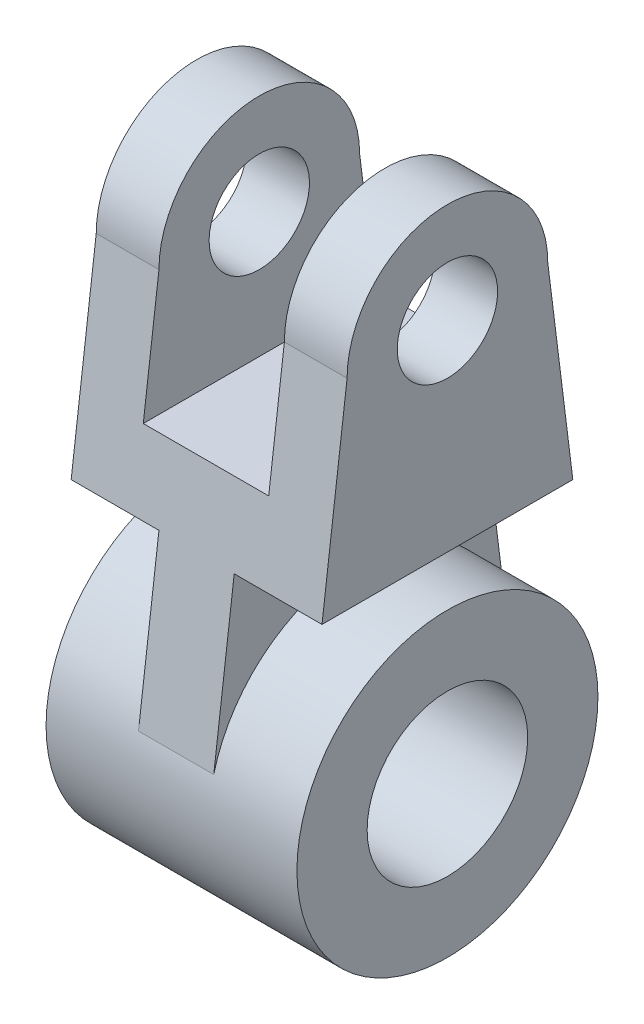
SolidWorks part; units mm, degrees
ref_plane "Front Plane" through (0, 0, 0) normal (0, 0, 1) x (1, 0, 0)
ref_plane "Top Plane" through (0, 0, 0) normal (0, 1, 0) x (1, 0, 0)
ref_plane "Right Plane" through (0, 0, 0) normal (1, 0, 0) x (0, 0, -1)
sketch "Sketch1" plane through (0, 0, 0) normal (1, 0, 0) x (0, 0, -1)
  circle A0 centre (0, 0) radius 30
  circle A1 centre (0, 0) radius 16
  dimension "D1" = 32
  dimension "D2" = 60
extrude "Boss-Extrude1" add sketch "Sketch1" along normal mid plane 50
sketch "Sketch2" plane through (0, 0, 0) normal (1, 0, 0) x (0, 0, -1)
  line L0 (0, 30) -> (0, 40)
  circle A0 centre (0, 0) radius 30 construction
  dimension "D1" = 10
ref_plane "Plane1" through (0, 40, 0) normal (0, 1, 0) x (1, 0, 0)
sketch "Sketch3" plane through (0, 40, 0) normal (0, 1, 0) x (1, 0, 0)
  line L1 (-25, 25) -> (25, 25)
  line L2 (-25, 25) -> (-25, -25)
  line L3 (-25, -25) -> (25, -25)
  line L4 (25, 25) -> (25, -25)
  line L5 (-25, 25) -> (25, -25) construction
  line L6 (-25, -25) -> (25, 25) construction
  point P0 (0, 0)
  dimension "D1" = 50
  dimension "D2" = 50
sketch "Sketch4" plane through (0, 0, 0) normal (1, 0, 0) x (0, 0, -1)
  line L1 (-20, 80) -> (-25, 40)
  line L2 (-25, 40) -> (25, 40) construction
  line L3 (-25, 40) -> (25, 40)
  line L4 (25, 40) -> (-25, 40) construction
  line L5 (25, 40) -> (-25, 40) construction
  line L6 (25, 40) -> (20, 80)
  circle A0 centre (0, 80) radius 10
  arc A1 (20, 80) -> (-20, 80) centre (0, 80) ccw
  dimension "D2" = 20
  dimension "D3" = 40
extrude "Boss-Extrude3" add sketch "Sketch4" along normal mid plane 50 separate body
sketch "Sketch5" plane through (0, 0, 0) normal (1, 0, 0) x (0, 0, -1)
  line L0 (-25, 40) -> (-30, 0)
  line L1 (-25, 40) -> (25, 40) construction
  line L2 (25, 40) -> (30, 0)
  line L3 (25, 40) -> (-25, 40) construction
  circle A0 centre (0, 0) radius 30 construction
sketch "Sketch7" plane through (0, 40, 0) normal (0, -1, 0) x (1, 0, 0)
  line L0 (-25, 25) -> (25, 25) construction
  line L1 (-7.5, -25) -> (7.5, -25)
  line L2 (-7.5, -25) -> (-7.5, 25)
  line L3 (-7.5, 25) -> (7.5, 25)
  line L4 (7.5, -25) -> (7.5, 25)
  line L5 (-7.5, -25) -> (7.5, 25) construction
  line L6 (-7.5, 25) -> (7.5, -25) construction
  point P0 (0, 0)
  dimension "D1" = 15
sketch "Sketch8" plane through (0, 0, 0) normal (0, 1, 0) x (1, 0, 0)
  line L0 (-25, -30) -> (25, -30) construction
  line L1 (-7.5, 30) -> (7.5, 30)
  line L2 (-7.5, 30) -> (-7.5, -30)
  line L3 (-7.5, -30) -> (7.5, -30)
  line L4 (7.5, 30) -> (7.5, -30)
  line L5 (-7.5, 30) -> (7.5, -30) construction
  line L6 (-7.5, -30) -> (7.5, 30) construction
  point P0 (0, 0)
  dimension "D1" = 15
loft "Loft1" add profiles "Sketch7", "Sketch8"
sketch "Sketch9" plane through (25, 0, 0) normal (1, 0, 0) x (0, 0, -1)
  circle A0 centre (0, 0) radius 16
extrude "Cut-Extrude1" cut sketch "Sketch9" against normal blind 50
sketch "Sketch11" plane through (0, 0, 0) normal (0, 0, 1) x (1, 0, 0)
  line L2 (25, 80) -> (-25, 80) construction
  line L3 (-12.5, 105) -> (12.5, 105)
  line L4 (-12.5, 105) -> (-12.5, 55)
  line L5 (-12.5, 55) -> (12.5, 55)
  line L6 (12.5, 105) -> (12.5, 55)
  line L7 (-12.5, 105) -> (12.5, 55) construction
  line L8 (-12.5, 55) -> (12.5, 105) construction
  point P5 (0, 80)
extrude "Cut-Extrude3" cut sketch "Sketch11" against normal mid plane 109
